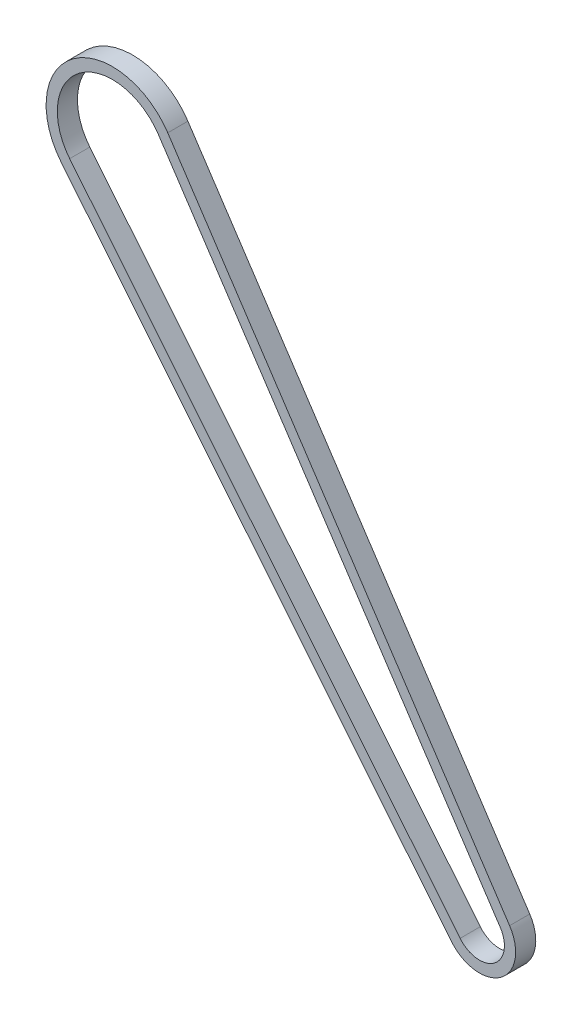
SolidWorks part; units mm, degrees
ref_plane "Front Plane" through (0, 0, 0) normal (0, 0, 1) x (1, 0, 0)
ref_plane "Top Plane" through (0, 0, 0) normal (0, 1, 0) x (1, 0, 0)
ref_plane "Right Plane" through (0, 0, 0) normal (1, 0, 0) x (0, 0, -1)
sketch "Sketch2" plane through (0, 0, 0) normal (0, 0, 1) x (1, 0, 0)
  line L0 (0, 0) -> (1, 0) construction
  line L1 (0, 0) -> (0, 1) construction
  line L2 (20.5254, 13.6052) -> (173.1848, -216.7037)
  line L3 (155.2574, -229.8882) -> (-19.103, -15.5392)
  arc A0 (-19.103, -15.5392) -> (20.5254, 13.6052) centre (0, 0) cw
  arc A1 (173.1848, -216.7037) -> (155.2574, -229.8882) centre (163.8994, -222.8585) cw
extrude "Extrude-Thin1" add sketch "Sketch2" against normal blind 9 thin thin type one direction wall 5
